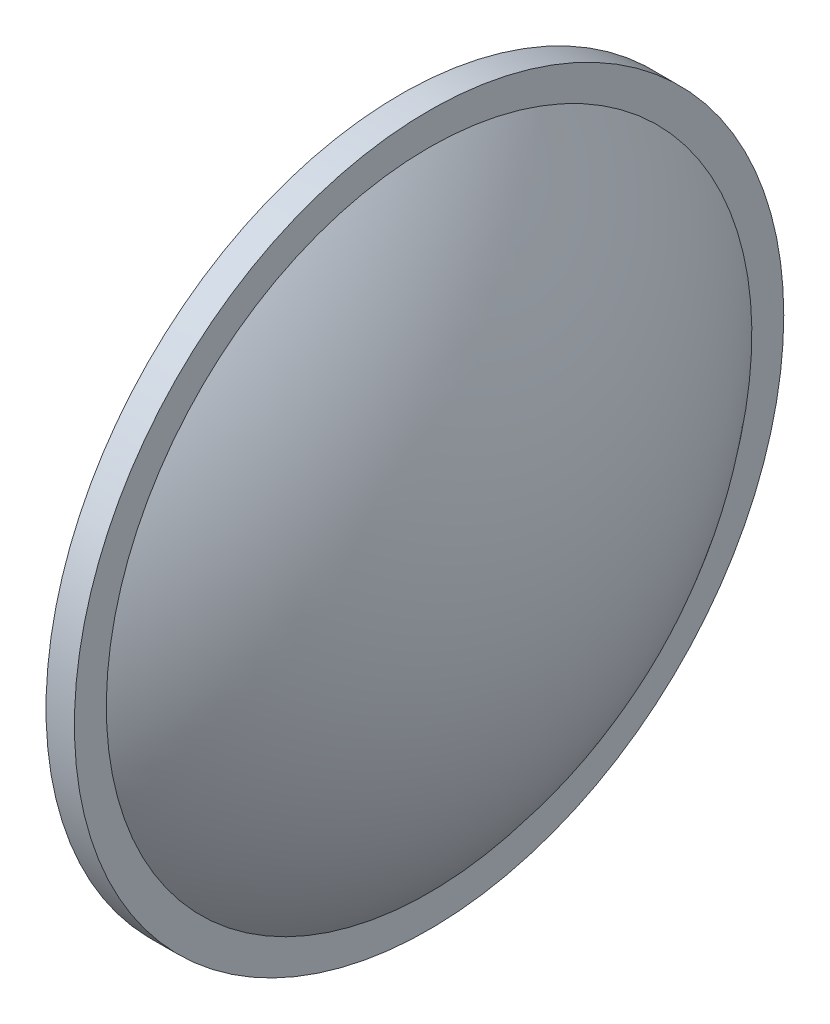
SolidWorks part; units mm, degrees
ref_plane "前视基准面" through (0, 0, 0) normal (0, 0, 1) x (1, 0, 0)
ref_plane "上视基准面" through (0, 0, 0) normal (0, 1, 0) x (1, 0, 0)
ref_plane "右视基准面" through (0, 0, 0) normal (1, 0, 0) x (0, 0, -1)
sketch "草图1" plane through (0, 0, 0) normal (1, 0, 0) x (0, 0, -1)
  circle A0 centre (0, 0) radius 50
  dimension "D1" = 100
extrude "凸台-拉伸1" add sketch "草图1" along normal blind 4
sketch "草图2" plane through (0, 0, 0) normal (0, 0, 1) x (1, 0, 0)
  line L0 (4, 0) -> (4, -45.5) construction
  line L1 (-49.6335, 0) -> (20.7, 0) construction
  line L2 (4, -50) -> (4, 50) construction
  line L3 (4, 0) -> (4, 50) construction
  line L4 (4, 0) -> (4, 45.5)
  line L5 (4, 0) -> (20.7, 0) construction
  line L6 (4, 45.5) -> (-2.7466, -52.4254) construction
  line L7 (4, 45.5) -> (4, 0)
  line L8 (20.7, 0) -> (4, 0)
  circle A1 centre (-49.6335, 0) radius 70.3335 construction
  arc A2 (4, 45.5) -> (-2.7466, -52.4254) centre (-49.6335, 0) cw construction
  arc A3 (4, 45.5) -> (20.7, 0) centre (-49.6335, 0) cw
  point P2 (4, 50)
  point P6 (4, 0)
  point P9 (4, 0)
  dimension "D1" = 45.5
  dimension "D2" = 16.7
revolve "旋转2" add sketch "草图2" angle 360 about L8
